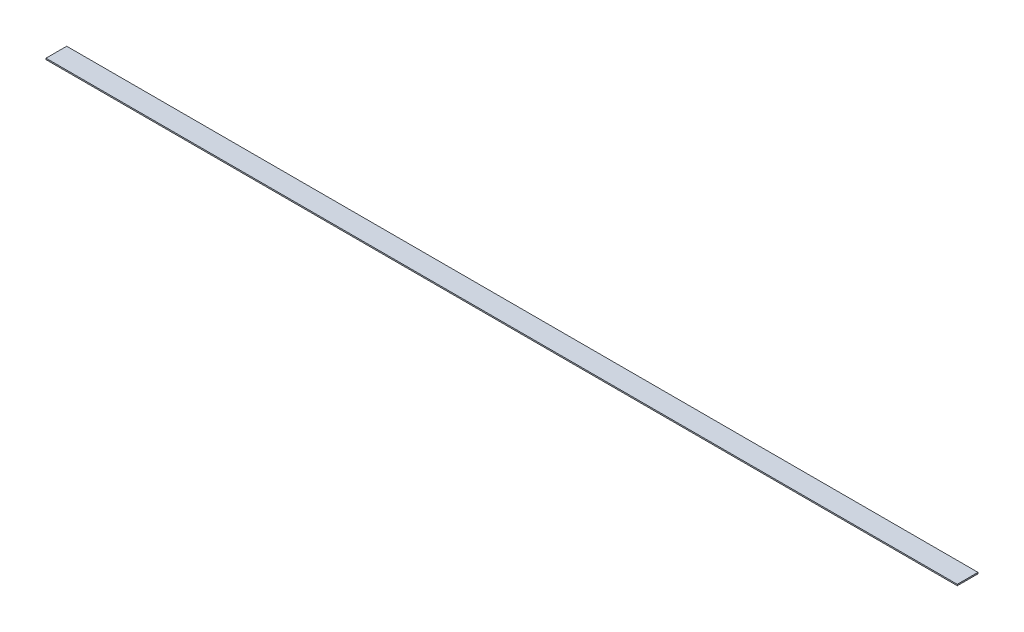
SolidWorks part; units mm, degrees
material "Very Low Density PE (SS)"
ref_plane "Front Plane" through (0, 0, 0) normal (0, 0, 1) x (1, 0, 0)
ref_plane "Top Plane" through (0, 0, 0) normal (0, 1, 0) x (1, 0, 0)
ref_plane "Right Plane" through (0, 0, 0) normal (1, 0, 0) x (0, 0, -1)
sketch "Sketch1" plane through (0, 0, 0) normal (0, 1, 0) x (1, 0, 0)
  line L1 (1117.6, -25.4) -> (-1117.6, -25.4)
  line L2 (1117.6, -25.4) -> (1117.6, 25.4)
  line L3 (1117.6, 25.4) -> (-1117.6, 25.4)
  line L4 (-1117.6, -25.4) -> (-1117.6, 25.4)
  line L5 (1117.6, -25.4) -> (-1117.6, 25.4) construction
  line L6 (1117.6, 25.4) -> (-1117.6, -25.4) construction
  point P0 (0, 0)
  dimension "D1" = 2235.2
  dimension "D2" = 50.8
extrude "Boss-Extrude1" add sketch "Sketch1" along normal blind 3.175
